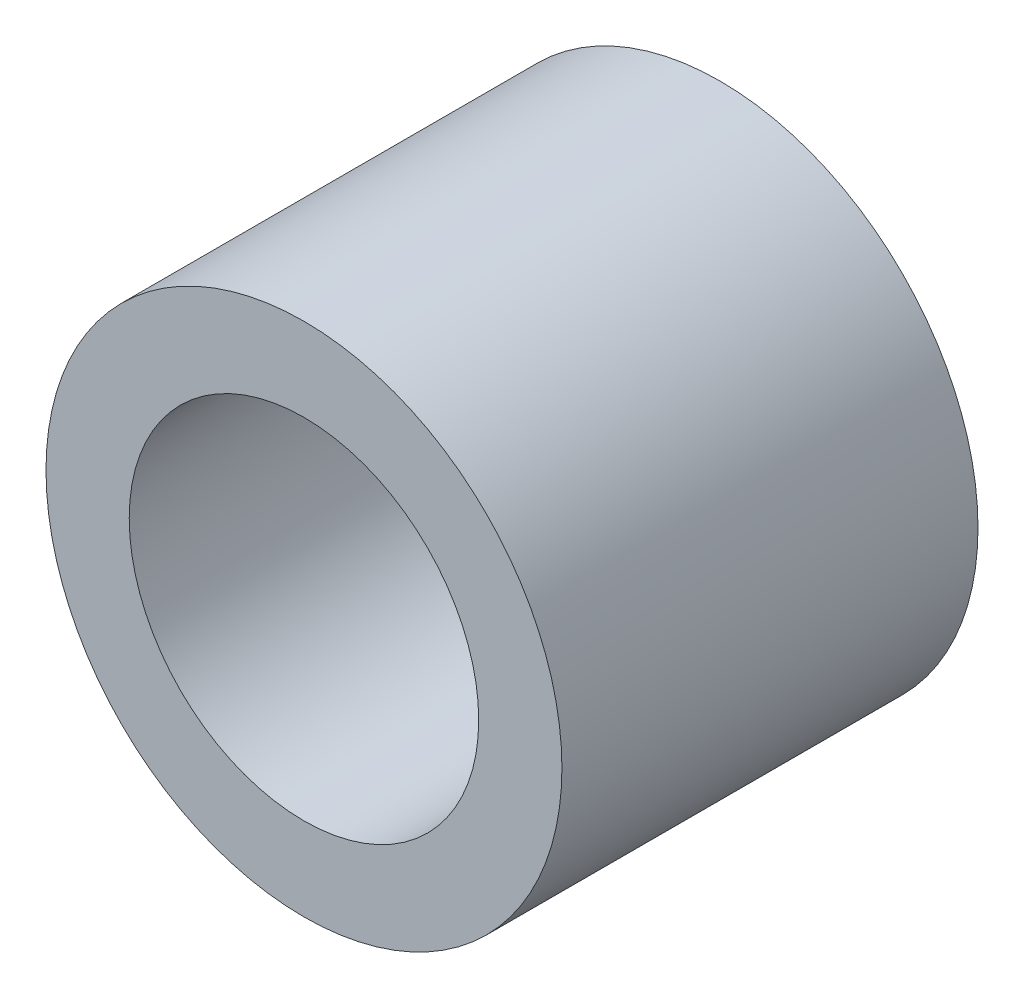
SolidWorks part; units mm, degrees
ref_plane "Front Plane" through (0, 0, 0) normal (0, 0, 1) x (1, 0, 0)
ref_plane "Top Plane" through (0, 0, 0) normal (0, 1, 0) x (1, 0, 0)
ref_plane "Right Plane" through (0, 0, 0) normal (1, 0, 0) x (0, 0, -1)
sketch "Sketch1" plane through (0, 0, 0) normal (0, 0, 1) x (1, 0, 0)
  circle A0 centre (0, 0) radius 2.1
  circle A1 centre (0, 0) radius 3.1
  dimension "D1" = 6.2
  dimension "D2" = 4.2
extrude "Boss-Extrude1" add sketch "Sketch1" along normal blind 5
